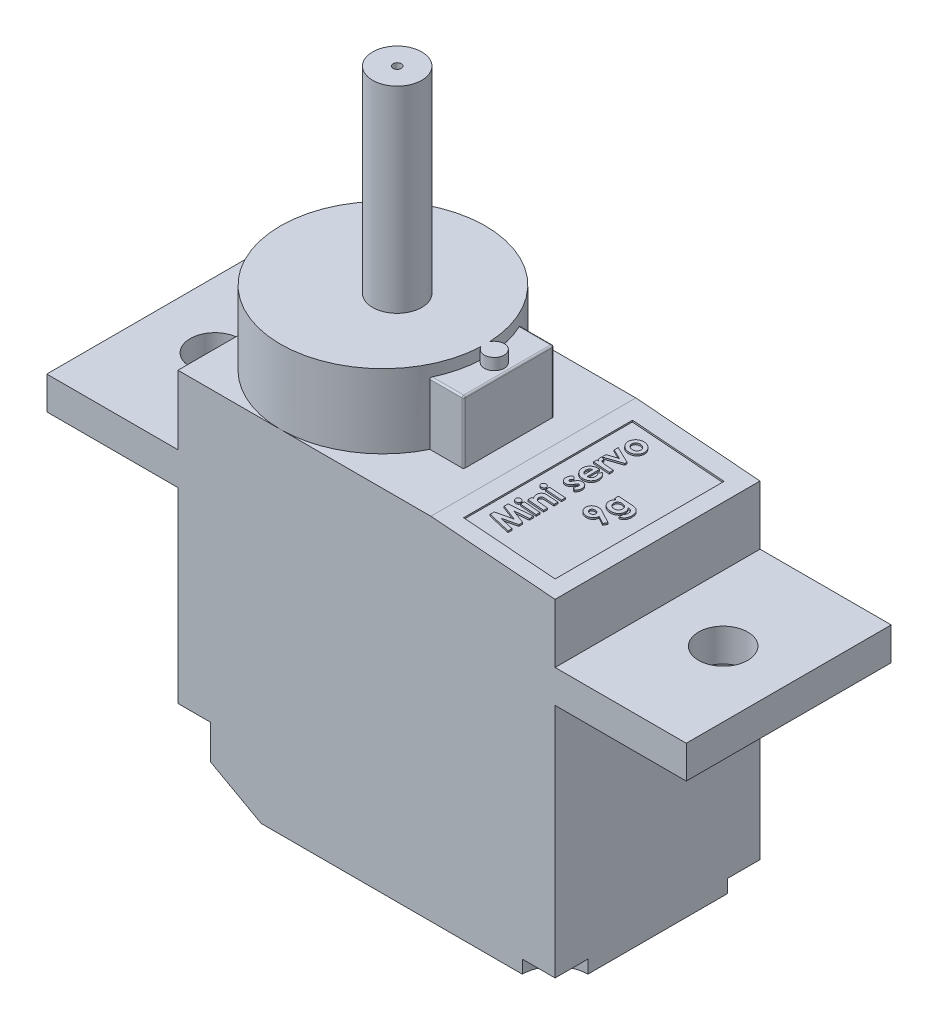
SolidWorks part; units mm, degrees
other "Camera1"
material "ABS"
ref_plane "Front Plane" through (0, 0, 0) normal (0, 0, 1) x (1, 0, 0)
ref_plane "Top Plane" through (0, 0, 0) normal (0, 1, 0) x (1, 0, 0)
ref_plane "Right Plane" through (0, 0, 0) normal (1, 0, 0) x (0, 0, -1)
sketch "Sketch1" plane through (0, 0, 0) normal (0, 1, 0) x (1, 0, 0)
  line L1 (11.5, -6.25) -> (-11.5, -6.25)
  line L2 (11.5, -6.25) -> (11.5, 6.25)
  line L3 (11.5, 6.25) -> (-11.5, 6.25)
  line L4 (-11.5, -6.25) -> (-11.5, 6.25)
  line L5 (11.5, -6.25) -> (-11.5, 6.25) construction
  line L6 (11.5, 6.25) -> (-11.5, -6.25) construction
  point P0 (0, 0)
  dimension "D1" = 12.5
  dimension "D2" = 23
extrude "Boss-Extrude1" add sketch "Sketch1" along normal blind 15.2
sketch "Sketch2" plane through (0, 15.2, 0) normal (0, 1, 0) x (1, 0, 0)
  line L0 (11.5, -6.25) -> (11.5, 6.25) construction
  line L1 (19.5, -6.25) -> (-19.5, -6.25)
  line L2 (19.5, -6.25) -> (19.5, 6.25)
  line L3 (19.5, 6.25) -> (-19.5, 6.25)
  line L4 (-19.5, -6.25) -> (-19.5, 6.25)
  line L5 (19.5, -6.25) -> (-19.5, 6.25) construction
  line L6 (19.5, 6.25) -> (-19.5, -6.25) construction
  point P0 (0, 0)
  dimension "D1" = 8
  dimension "D2" = 12.5
extrude "Boss-Extrude2" add sketch "Sketch2" along normal blind 2
sketch "Sketch3" plane through (0, 17.2, 0) normal (0, 1, 0) x (1, 0, 0)
  line L0 (19.5, 6.25) -> (-19.5, 6.25) construction
  line L1 (11.5, -6.25) -> (-11.5, -6.25)
  line L2 (11.5, -6.25) -> (11.5, 6.25)
  line L3 (11.5, 6.25) -> (-11.5, 6.25)
  line L4 (-11.5, -6.25) -> (-11.5, 6.25)
  line L5 (11.5, -6.25) -> (-11.5, 6.25) construction
  line L6 (11.5, 6.25) -> (-11.5, -6.25) construction
  point P0 (0, 0)
  dimension "D1" = 23
extrude "Boss-Extrude3" add sketch "Sketch3" along normal blind 4.2
sketch "Sketch4" plane through (0, 0, 6.25) normal (0, 0, 1) x (1, 0, 0)
  line L0 (11.5, 20.8) -> (3.9237, 21.4)
  line L1 (11.5, 21.4) -> (11.5, 17.2) construction
  line L2 (-11.5, 21.4) -> (11.5, 21.4) construction
  line L3 (3.9237, 21.4) -> (11.5, 21.4)
  line L4 (11.5, 21.4) -> (11.5, 20.8)
  dimension "D1" = 3.6
  dimension "D2" = 7.6
extrude "Cut-Extrude1" cut sketch "Sketch4" against normal through all
sketch "Sketch5" plane through (0, 21.4, 0) normal (0, 1, 0) x (1, 0, 0)
  line L0 (3.9237, 6.25) -> (-11.5, 6.25) construction
  line L2 (-11.5, 6.25) -> (-11.5, -6.25) construction
  line L3 (-11.5, -6.25) -> (3.9237, -6.25) construction
  circle A0 centre (-5.25, 0) radius 6.25
extrude "Boss-Extrude4" add sketch "Sketch5" along normal blind 4.5
sketch "Sketch6" plane through (0, 21.4, 0) normal (0, 1, 0) x (1, 0, 0)
  line L0 (3.9237, 6.25) -> (3.9237, -6.25) construction
  line L1 (-2.4237, -2.75) -> (2.4237, -2.75)
  line L2 (-2.4237, -2.75) -> (-2.4237, 2.75)
  line L3 (-2.4237, 2.75) -> (2.4237, 2.75)
  line L4 (2.4237, -2.75) -> (2.4237, 2.75)
  line L5 (-2.4237, -2.75) -> (2.4237, 2.75) construction
  line L6 (-2.4237, 2.75) -> (2.4237, -2.75) construction
  point P0 (0, 0)
  dimension "D1" = 1.5
  dimension "D2" = 5.5
extrude "Boss-Extrude5" add sketch "Sketch6" along normal blind 3.8
sketch "Sketch7" plane through (0, 25.2, 0) normal (0, 1, 0) x (1, 0, 0)
  circle A0 centre (1.5423, 0) radius 0.6059
extrude "Boss-Extrude7" add sketch "Sketch7" along normal up to surface (0.7 mm away) up to face at (-5.25, 25.9, 6.25)
sketch "Sketch8" plane through (0, 25.9, 0) normal (0, 1, 0) x (1, 0, 0)
  circle A0 centre (-4.3789, 0) radius 1.5
extrude "Boss-Extrude8" add sketch "Sketch8" along normal blind 12
sketch "Sketch9" plane through (0, 0, 6.25) normal (0, 0, 1) x (1, 0, 0)
  line L0 (-11.5, 0) -> (-6.4206, 0)
  line L1 (-11.5, 0) -> (11.5, 0) construction
  line L2 (-6.4206, 0) -> (-11.5, 2.8)
  line L3 (-11.5, 15.2) -> (-11.5, 0) construction
  line L4 (-11.5, 2.8) -> (-11.5, 0)
  dimension "D1" = 5.8
  dimension "D2" = 2.8
extrude "Cut-Extrude2" cut sketch "Sketch9" against normal through all
sketch "Sketch13" plane through (0, 37.9, 0) normal (0, 1, 0) x (1, 0, 0)
  circle A0 centre (-4.3789, 0) radius 0.25
  dimension "D1" = 0.5
extrude "Cut-Extrude3" cut sketch "Sketch13" against normal up to surface (16.5 mm away) up to face at (-9.8481, 21.4, 4.5981)
sketch "Sketch15" plane through (0, 0, 0) normal (0, -1, 0) x (1, 0, 0)
  line L0 (11.5, 6.25) -> (11.5, -6.25) construction
  line L1 (-6.4206, 6.25) -> (11.5, 6.25) construction
  line L2 (9.5, 6.25) -> (11.5, 6.25)
  line L3 (11.5, 6.25) -> (11.5, 4.25)
  line L4 (4.5258, 0) -> (-4.7559, 0) construction
  line L5 (11.5, -6.25) -> (11.5, -4.25)
  line L6 (9.5, -6.25) -> (11.5, -6.25)
  arc A0 (11.5, 4.25) -> (9.5, 6.25) centre (11.5, 6.25) cw
  arc A1 (11.5, -4.25) -> (9.5, -6.25) centre (11.5, -6.25) ccw
  dimension "D1" = 2
extrude "Cut-Extrude12" cut sketch "Sketch15" against normal blind 0.8
sketch "Sketch16" plane through (0, 0, 0) normal (0, -1, 0) x (1, 0, 0)
  line L0 (-6.4206, 6.25) -> (-11.5, 6.25) construction
  line L1 (-11.5, -6.25) -> (-11.5, 6.25) construction
  line L2 (-11.5, -6.25) -> (-11.5, 6.25) construction
  line L3 (-11.5, 4.25) -> (-11.5, 6.25)
  line L4 (-11.5, 6.25) -> (-9.5, 6.25)
  line L5 (-1.3995, 0) -> (2.6342, 0) construction
  line L6 (-11.5, -6.25) -> (-9.5, -6.25)
  line L7 (-11.5, -4.25) -> (-11.5, -6.25)
  arc A0 (-9.5, 6.25) -> (-11.5, 4.25) centre (-11.5, 6.25) cw
  arc A1 (-9.5, -6.25) -> (-11.5, -4.25) centre (-11.5, -6.25) ccw
  dimension "D1" = 2
extrude "Cut-Extrude13" cut sketch "Sketch16" against normal blind 3.8
sketch "Sketch17" plane through (1.7087, 21.5754, 0) normal (0.0789, 0.9969, 0) x (0.9969, -0.0789, 0)
  line L1 (8.822, -5.25) -> (3.222, -5.25)
  line L2 (8.822, -5.25) -> (8.822, 5.05)
  line L3 (8.822, 5.05) -> (3.222, 5.05)
  line L4 (3.222, -5.25) -> (3.222, 5.05)
  line L8 (2.222, 6.25) -> (2.222, -6.25) construction
  line L9 (9.822, 6.25) -> (9.822, -6.25) construction
  line L10 (2.222, -6.25) -> (9.822, -6.25) construction
  dimension "D1" = 1
  dimension "D2" = 1
  dimension "D3" = 1
  dimension "D4" = 10.3
extrude "Cut-Extrude14" cut sketch "Sketch17" against normal blind 0.1
sketch "Sketch19" plane through (1.7008, 21.4757, 0) normal (0.0789, 0.9969, 0) x (0.9969, -0.0789, 0)
  line L0 (5.1279, -5.25) -> (5.1279, 5.05) construction
  line L4 (3.222, -5.25) -> (8.822, -5.25) construction
  line L5 (8.822, 5.05) -> (3.222, 5.05) construction
  line L6 (7.5214, 5.05) -> (7.5214, -5.25) construction
  text T0 "<b>Mini servo</b>" font "Century Gothic" height in points 5
  text T1 "<b>9g</b>" font "Century Gothic" height in points 5
extrude "Boss-Extrude9" add sketch "Sketch19" along normal up to surface (0.1 mm away) up to face at (7.7119, 21.1, 0.1)
fillet "Fillet3" radius 0.1 5 edges at (2.4237, 25.2, 0) (1.3931, 25.2, 2.75) (2.4237, 23.3, 2.75) (2.4237, 23.3, -2.75) (1.3931, 25.2, -2.75)
hole_wizard "Ø3.0 (3) Diameter Hole1" positions "Sketch23" profile "Sketch20" hole size "Ø3.0" standard "ISO" end condition through all
sketch "Sketch23" plane through (0, 17.2, 0) normal (0, 1, 0) x (1, 0, 0)
  line L0 (-11.5, 6.25) -> (-11.5, 0) construction
  point P0 (-15.5, 0)
  dimension "D1" = 4
sketch "Sketch20" plane through (-15.5, 17.2, 0) normal (1, 0, 0) x (0, 0, 1)
  line L0 (0, 0) -> (0, 17.2)
  line L1 (0, 17.2) -> (1.5, 17.2)
  line L2 (1.5, 17.2) -> (1.5, 0)
  line L5 (1.5, 0) -> (0, 0)
  line L11 (0, -6.35) -> (0, 107.95) construction
  dimension "Thru Hole Dia." = 3
  dimension "Thru Hole Depth" = 17.2
mirror "Mirror1" about plane through (0, 0, 0) normal (1, 0, 0) of "Ø3.0 (3) Diameter Hole1"
